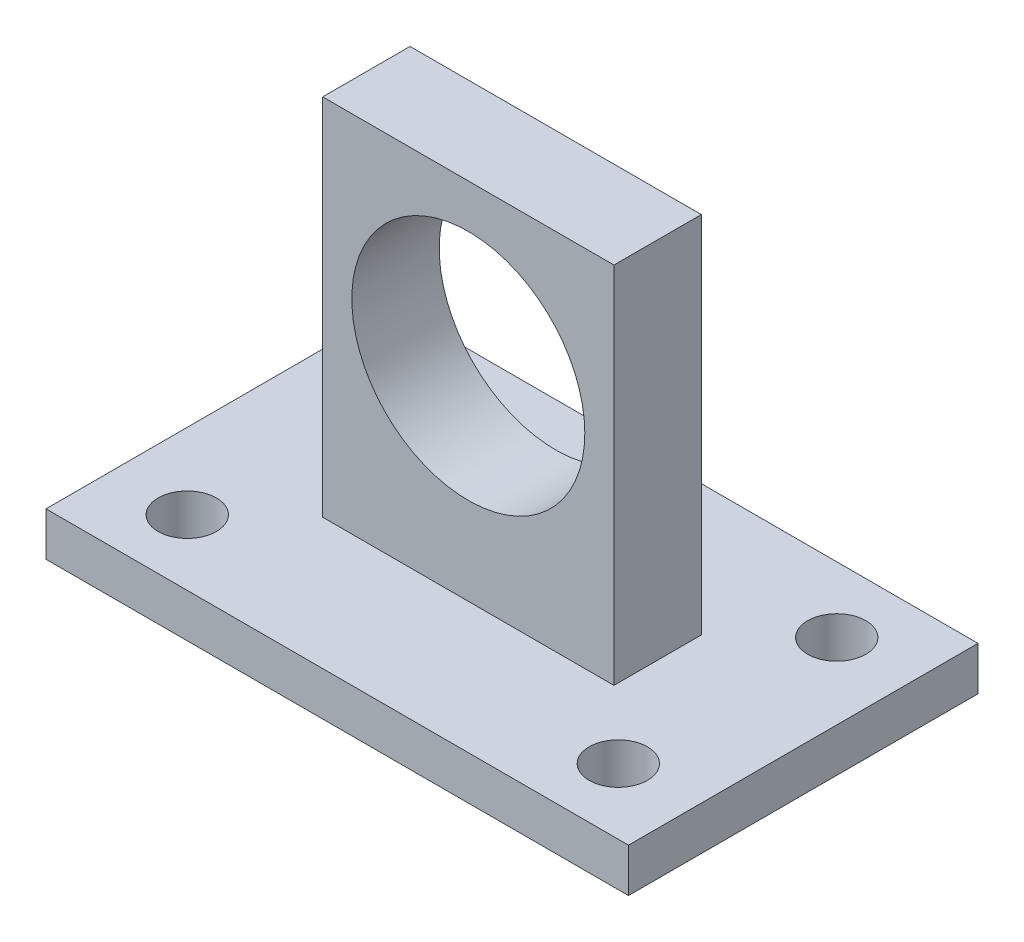
SolidWorks part; units mm, degrees
material "ABS"
ref_plane "Front" through (0, 0, 0) normal (0, 0, 1) x (1, 0, 0)
ref_plane "Top" through (0, 0, 0) normal (0, 1, 0) x (1, 0, 0)
ref_plane "Right" through (0, 0, 0) normal (1, 0, 0) x (0, 0, -1)
sketch "草图1" plane through (0, 0, 0) normal (0, 1, 0) x (1, 0, 0)
  line L0 (0, 0) -> (0, 12) construction
  line L1 (0, 0) -> (20, 0) construction
  line L2 (-20, 12) -> (20, 12)
  line L3 (20, 12) -> (20, -12)
  line L4 (-20, 12) -> (-20, -12)
  line L5 (-20, -12) -> (20, -12)
  line L6 (0, 0) -> (0, -7.5) construction
  line L7 (0, -7.5) -> (-14.8, -7.5) construction
  circle A0 centre (-14.8, -7.5) radius 2
  circle A1 centre (14.8, -7.5) radius 2
  circle A2 centre (-14.8, 7.5) radius 2
  circle A3 centre (14.8, 7.5) radius 2
  point P9 (-20, 0)
extrude "凸台-拉伸1" add sketch "草图1" along normal blind 3
sketch "草图2" plane through (0, 3, 0) normal (0, 1, 0) x (1, 0, 0)
  line L0 (0, 0) -> (0, 3) construction
  line L1 (0, 3) -> (20, 3) construction
  line L2 (20, -12) -> (20, 12) construction
  line L3 (20, 3) -> (20, -3) construction
  line L10 (0, 0) -> (0, -3) construction
  line L11 (0, -3) -> (-10, -3) construction
  line L12 (-10, -3) -> (-10, 3) construction
  line L14 (-10, 3) -> (-10, -3)
  line L15 (-10, -3) -> (10, -3)
  line L17 (-10, 3) -> (10, 3)
  line L18 (10, 3) -> (10, -3)
extrude "凸台-拉伸2" add sketch "草图2" along normal blind 25
sketch "草图3" plane through (0, 0, 3) normal (0, 0, 1) x (1, 0, 0)
  line L0 (0, 3) -> (0, 17) construction
  line L1 (-20, 3) -> (20, 3) construction
  circle A1 centre (0, 17) radius 8
extrude "切除-拉伸1" cut sketch "草图3" against normal blind 10
